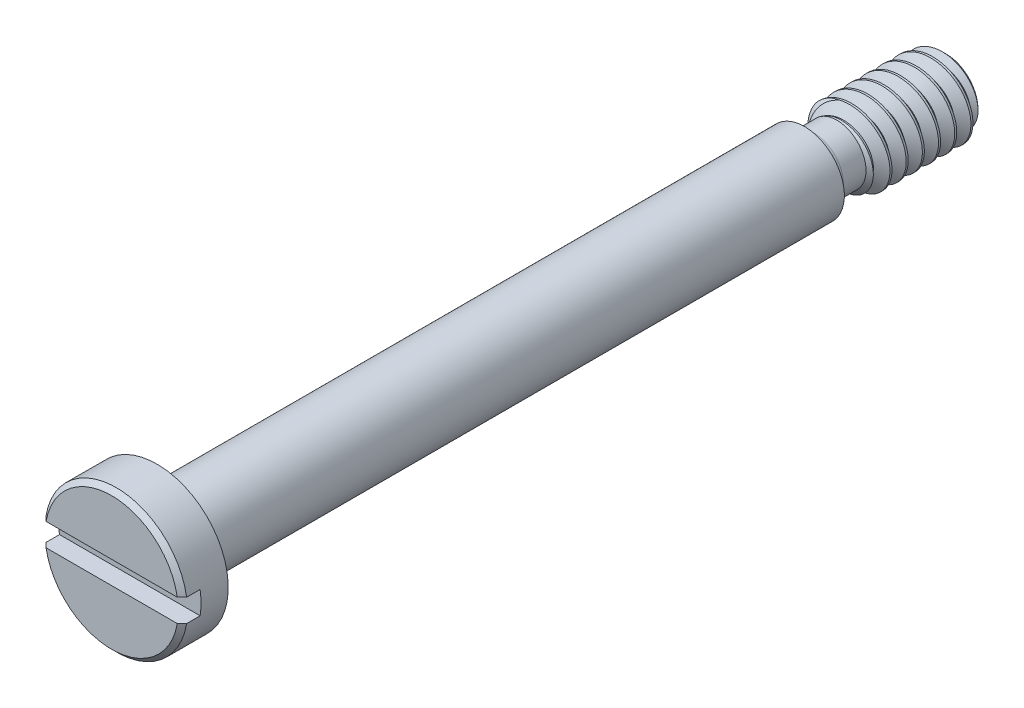
SolidWorks part; units mm, degrees
other "DetailItem1"
other "DetailItem2"
other "DetailItem5"
other "DetailItem6"
ref_plane "Front" through (0, 0, 0) normal (0, 0, 1) x (1, 0, 0)
ref_plane "Top" through (0, 0, 0) normal (0, 1, 0) x (1, 0, 0)
ref_plane "Right" through (0, 0, 0) normal (1, 0, 0) x (0, 0, -1)
sketch "Sketch1" plane through (0, 0, 0) normal (1, 0, 0) x (0, 0, -1)
  line L0 (-8.1836, 1.397) -> (-7.2946, 1.397)
  line L1 (-7.2946, 1.397) -> (-7.2946, 0.781)
  line L2 (-7.2946, 0.781) -> (5.4054, 0.781)
  line L3 (5.4054, 0.781) -> (5.4054, 0.762)
  line L4 (5.4054, 0.762) -> (8.1836, 0.762)
  line L5 (8.1836, 0.762) -> (8.1836, 0)
  line L6 (8.1836, 0) -> (-8.1836, 0)
  line L7 (-8.1836, 0) -> (-8.1836, 1.397)
  line L8 (-8.1836, 1.397) -> (-8.1836, -1.397) construction
  line L9 (8.1836, 0.762) -> (8.1836, -0.762) construction
  line L10 (5.4054, 0.781) -> (5.4054, -0.781) construction
  point P12 (5.4054, 0)
  dimension "Head Dia" = 2.794
  dimension "Head Ht" = 0.889
  dimension "Thread Lg" = 2.7781
  dimension "Thread Dia" = 1.524
  dimension "Shoulder Dia" = 1.5621
  dimension "Shoulder Lg" = 12.7
sketch "Sketch12" plane through (0, 0, 0) normal (1, 0, 0) x (0, 0, -1)
  line L0 (-7.2946, 1.397) -> (-7.2946, 0.781) construction
  line L1 (-8.1836, 1.397) -> (-7.2946, 1.397) construction
  line L2 (-8.1836, 0) -> (-8.1836, 1.397) construction
  line L3 (8.1836, 0) -> (-8.1836, 0) construction
  line L4 (8.1836, 0.762) -> (8.1836, 0) construction
  line L5 (5.4054, 0.762) -> (8.1836, 0.762) construction
  line L6 (5.4054, 0.781) -> (5.4054, 0.762) construction
  line L7 (-7.2946, 0.781) -> (5.4054, 0.781) construction
  line L8 (-7.2946, 1.397) -> (-7.2946, 0.781)
  line L9 (-8.1836, 1.397) -> (-7.2946, 1.397)
  line L10 (-8.1836, 0) -> (-8.1836, 1.397)
  line L11 (8.1836, 0) -> (-8.1836, 0)
  line L12 (8.1836, 0.762) -> (8.1836, 0)
  line L13 (5.4054, 0.762) -> (8.1836, 0.762)
  line L14 (5.4054, 0.781) -> (5.4054, 0.762)
  line L15 (-7.2946, 0.781) -> (5.4054, 0.781)
revolve "Revolve1" add sketch "Sketch12" angle 360 about L6
sketch "Sketch5" plane through (0, 0, 0) normal (1, 0, 0) x (0, 0, -1)
  line L0 (5.4054, 0.781) -> (6.25, 0.781)
  line L1 (6.25, 0.781) -> (6.0404, 0.5715)
  line L2 (6.0404, 0.5715) -> (5.5959, 0.5715)
  line L3 (5.4054, 0.781) -> (5.4054, 0.762)
  line L5 (5.4054, 0.762) -> (8.1836, 0.762) construction
  line L6 (8.1836, 0) -> (6.0404, 0) construction
  line L7 (7.112, 0) -> (7.112, -0.762) construction
  arc A0 (5.4054, 0.762) -> (5.5959, 0.5715) centre (5.5959, 0.762) ccw
  dimension "CADB" = 0.635
  dimension "D3" = 45
  dimension "CADA" = 1.143
revolve "Cut-Revolve1" cut sketch "Sketch5" angle 360 about L6
ref_plane "Plane1" through (0, 0, -6.0404) normal (0, 0, 1) x (1, 0, 0)
sketch "Sketch8" plane through (0, 0, 8.1836) normal (0, 0, 1) x (1, 0, 0)
  line L0 (-1.397, 0.2235) -> (1.397, -0.2235) construction
  line L1 (-1.397, 0.2235) -> (1.397, 0.2235)
  line L2 (-1.397, 0.2235) -> (-1.397, -0.2235)
  line L3 (-1.397, -0.2235) -> (1.397, -0.2235)
  line L4 (1.397, 0.2235) -> (1.397, -0.2235)
  circle A1 centre (0, 0) radius 1.397 construction
  dimension "D1" = 0.447
extrude "Cut-Extrude2" cut sketch "Sketch8" against normal blind 0.3556
sketch "Sketch9" plane through (0, 0, -8.1836) normal (0, 0, -1) x (-1, 0, 0)
  circle A1 centre (0, 0) radius 0.762 construction
  circle A2 centre (0, 0) radius 0.762
curve "Helix/Spiral2" pitch 0.3175 height 2.7781 turns 8.75 parameters "Pitch"=0.3175
chamfer "Chamfer1" distance 0.0908 angle 45 2 edges at (0, -1.397, 8.1836) (0, 1.397, 8.1836)
chamfer "Chamfer2" distance 0.1372 angle 45 1 edges at (-0.762, 0, -8.1836)
sketch "Sketch11" plane through (0, 0, 0) normal (0, 0, 1) x (1, 0, 0)
  circle A0 centre (0, 0) radius 1.397
split "Split2" trim tools "Plane1" bodies to split 119 resulting bodies 127 131
sketch "Sketch10" plane through (0, 0, 0) normal (1, 0, 0) x (0, 0, -1)
  line L0 (8.1637, 0.7964) -> (8.3225, 0.5214) construction
  line L1 (8.3225, 0.5214) -> (8.4812, 0.7964) construction
  line L2 (8.4812, 0.7964) -> (8.1637, 0.7964) construction
  line L3 (8.1836, 0.762) -> (8.4614, 0.762) construction
  line L4 (8.3225, 0.7964) -> (8.3225, 0.762) construction
  line L5 (8.3225, 0.762) -> (8.3225, 0.5558) construction
  line L8 (8.3225, 0.5558) -> (8.3225, 0.5214) construction
  line L9 (8.3026, 0.5558) -> (8.3423, 0.5558)
  line L10 (8.1736, 0.7792) -> (8.4713, 0.7792)
  line L11 (8.3423, 0.5558) -> (8.4713, 0.7792)
  line L12 (8.3026, 0.5558) -> (8.1736, 0.7792)
  point P12 (8.3225, 0.7792)
  dimension "D1" = 0.3175
  dimension "D2" = 0.0397
sweep "Cut-Sweep1" cut profiles "Sketch10" path "Helix/Spiral2"
combine bodies "Combine1" operation type add bodies to combine 132 127
equation "\"D1@Chamfer1\" = \"Thread Dia@Sketch1\" * .125"
equation "\"D1@Cut-Extrude2\"= \"Head Ht@Sketch1\" * .4"
equation "\"D1@Chamfer2\" = \"Head Dia@Sketch1\" * .0325"
equation "\"D1@Sketch8\" = \"Head Dia@Sketch1\" * .16"
equation "\"D1@Chamfer1\"=\"Head Dia@Sketch1\"*.0325"
equation "\"D1@Chamfer2\"=\"Thread Dia@Sketch1\"*.09"
equation "\"D2@Sketch10\" = \"Pitch@Helix/Spiral2\" / 8"
equation "\"D1@Sketch10\" = \"Pitch@Helix/Spiral2\""
equation "\"D3@Helix/Spiral2\"=\"Thread Lg@Sketch1\""
